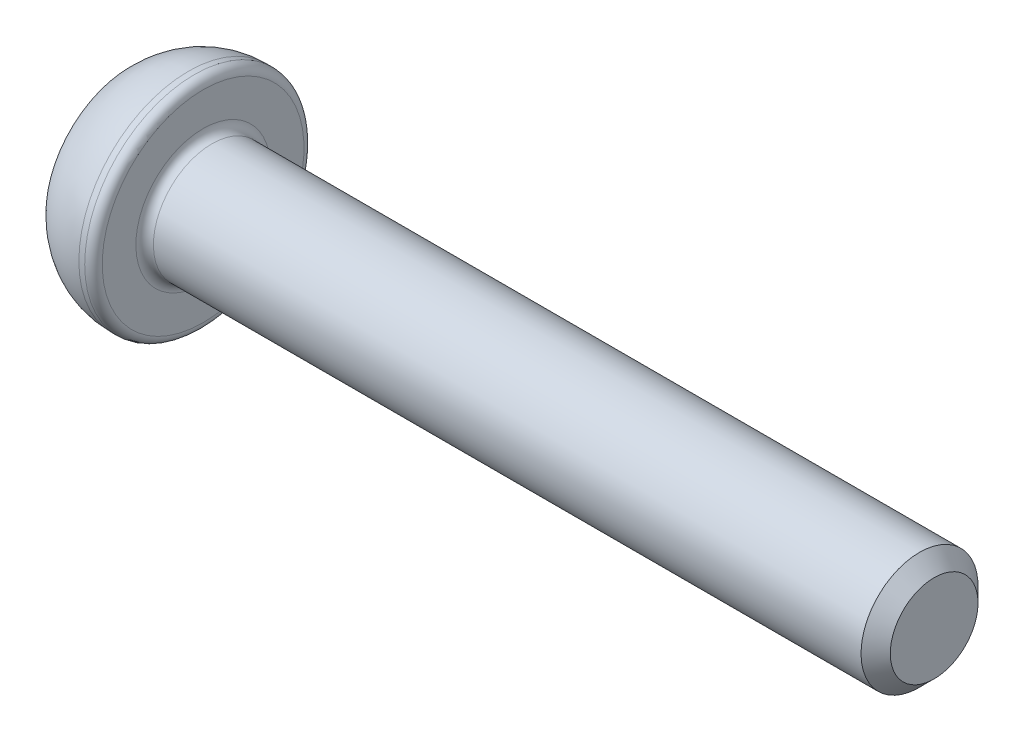
SolidWorks part; units mm, degrees
ref_plane "Спереди" through (0, 0, 0) normal (0, 0, 1) x (1, 0, 0)
ref_plane "Сверху" through (0, 0, 0) normal (0, 1, 0) x (1, 0, 0)
ref_plane "Справа" through (0, 0, 0) normal (1, 0, 0) x (0, 0, -1)
sketch "Эскиз1" plane through (0, 0, 0) normal (0, 0, 1) x (1, 0, 0)
  line L0 (0, 0) -> (0, 2.875)
  line L1 (2, 3.75) -> (2.5, 3.75)
  line L2 (2.5, 3.75) -> (2.5, 2)
  line L3 (2.5, 2) -> (27.5, 2)
  line L4 (27.5, 2) -> (27.5, 0)
  line L5 (27.5, 0) -> (0, 0) construction
  line L6 (0, 0) -> (27.5, 0)
  arc A0 (0, 2.875) -> (2, 3.75) centre (2, 1.0268) cw
  point P9 (2.5, 2.875)
  dimension "D1" = 0.5
  dimension "D2" = 4
  dimension "D3" = 7.5
  dimension "D5" = 2.5
  dimension "D6" = 25
revolve "Повернуть1" add sketch "Эскиз1" angle 360 about L5
cosmetic thread "Условное изображение резьбы1" parameters "D2"=3.22
sketch "Эскиз2" plane through (0, 0, 0) normal (-1, 0, 0) x (0, 0, 1)
  line L1 (0.7217, 1.25) -> (-0.7217, 1.25)
  line L2 (-0.7217, 1.25) -> (-1.4434, 0)
  line L3 (-1.4434, 0) -> (-0.7217, -1.25)
  line L4 (-0.7217, -1.25) -> (0.7217, -1.25)
  line L5 (0.7217, -1.25) -> (1.4434, 0)
  line L6 (1.4434, 0) -> (0.7217, 1.25)
  circle A0 centre (0, 0) radius 1.25 construction
  dimension "D1" = 2.5
extrude "Вырез-Вытянуть1" cut sketch "Эскиз2" against normal blind 1.5
fillet "Скругление1" radius 0.3 2 edges at (2.5, 2, 0) (2.5, 3.75, 0)
chamfer "Фаска1" distance 0.5 angle 45 1 edges at (27.5, 2, 0)
